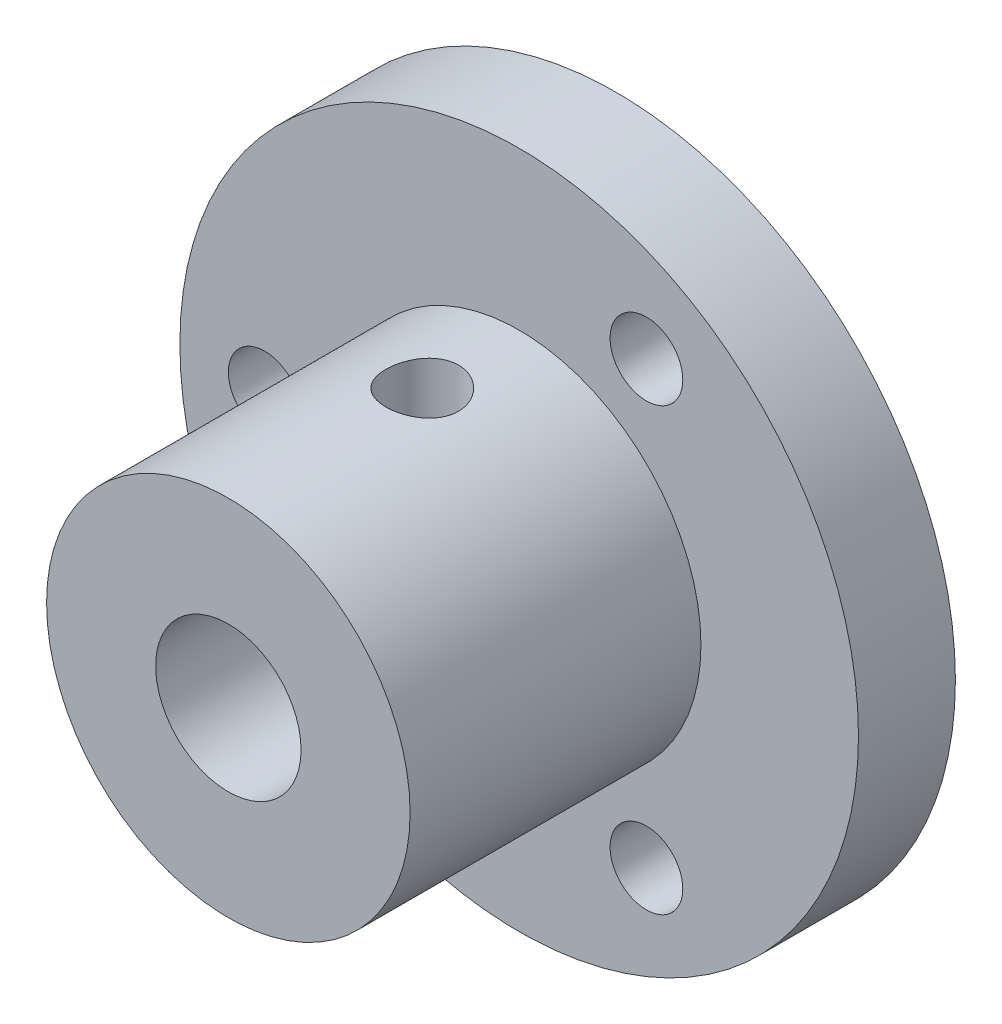
SolidWorks part; units mm, degrees
ref_plane "正面" through (0, 0, 0) normal (0, 0, 1) x (1, 0, 0)
ref_plane "平面" through (0, 0, 0) normal (0, 1, 0) x (1, 0, 0)
ref_plane "右側面" through (0, 0, 0) normal (1, 0, 0) x (0, 0, -1)
sketch "ｽｹｯﾁ1" plane through (0, 0, 0) normal (0, 0, 1) x (1, 0, 0)
  line L0 (-10.5, 0) -> (5.25, -9.0933) construction
  line L1 (5.25, -9.0933) -> (5.25, 9.0933) construction
  line L2 (5.25, 9.0933) -> (-10.5, 0) construction
  circle A0 centre (0, 0) radius 10.5 construction
  circle A2 centre (0, 0) radius 14
  circle A3 centre (-10.5, 0) radius 1.5
  circle A4 centre (5.25, -9.0933) radius 1.5
  circle A5 centre (5.25, 9.0933) radius 1.5
  circle A6 centre (0, 0) radius 3
  dimension "D1" = 21
  dimension "D2" = 3
  dimension "D3" = 28
  dimension "D4" = 6
extrude "ﾎﾞｽ - 押し出し1" add sketch "ｽｹｯﾁ1" along normal blind 4
sketch "ｽｹｯﾁ3" plane through (0, 0, 4) normal (0, 0, 1) x (1, 0, 0)
  circle A0 centre (0, 0) radius 7.5
  circle A1 centre (0, 0) radius 3
  circle A2 centre (0, 0) radius 3 construction
  dimension "D1" = 15
extrude "ﾎﾞｽ - 押し出し2" add sketch "ｽｹｯﾁ3" along normal blind 12
sketch "ｽｹｯﾁ4" plane through (0, 0, 0) normal (0, 1, 0) x (1, 0, 0)
  line L0 (0, -16) -> (0, 0) construction
  line L1 (-7.5, -16) -> (7.5, -16) construction
  circle A0 centre (0, -8) radius 1.5
  dimension "D1" = 8
  dimension "D2" = 3
extrude "ｶｯﾄ - 押し出し1" cut sketch "ｽｹｯﾁ4" along normal through all both and the other way through all
